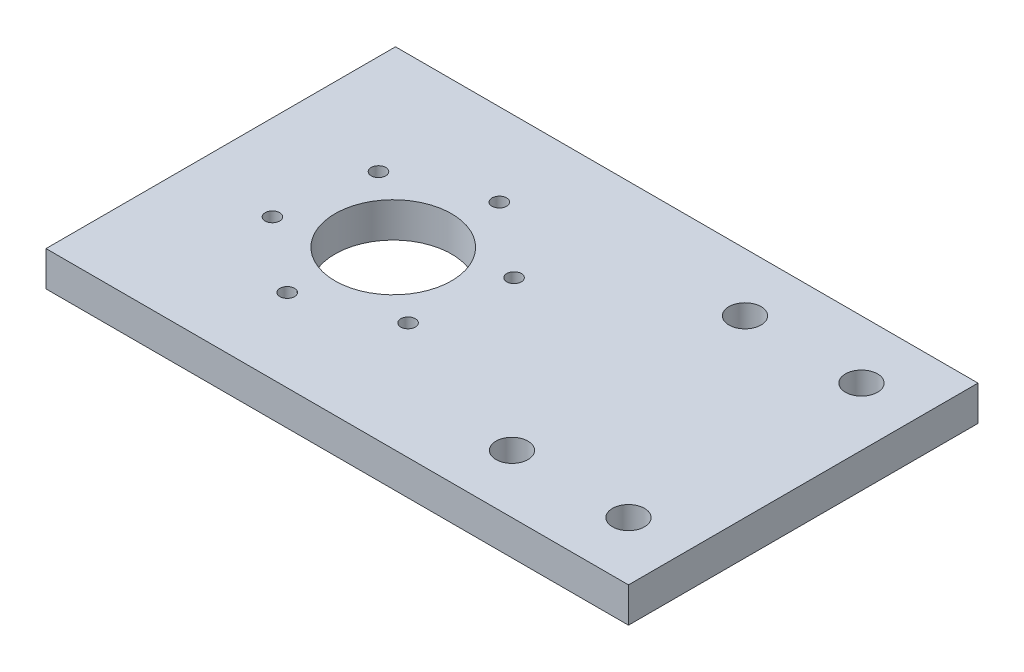
SolidWorks part; units mm, degrees
ref_plane "Front Plane" through (0, 0, 0) normal (0, 0, 1) x (1, 0, 0)
ref_plane "Top Plane" through (0, 0, 0) normal (0, 1, 0) x (1, 0, 0)
ref_plane "Right Plane" through (0, 0, 0) normal (1, 0, 0) x (0, 0, -1)
sketch "Sketch1" plane through (0, 0, 0) normal (0, 1, 0) x (1, 0, 0)
  line L1 (0, 0) -> (100, 0)
  line L2 (0, 0) -> (0, 60)
  line L3 (0, 60) -> (100, 60)
  line L4 (100, 0) -> (100, 60)
  dimension "D1" = 100
  dimension "D2" = 60
extrude "Boss-Extrude1" add sketch "Sketch1" along normal blind 6
sketch "Sketch2" plane through (0, 6, 0) normal (0, 1, 0) x (1, 0, 0)
  line L1 (100, 0) -> (100, 60) construction
  line L7 (100, 30) -> (0, 30) construction
  line L8 (0, 60) -> (0, 0) construction
  circle A0 centre (29.6153, 30) radius 10
  circle A5 centre (70, 50) radius 2.75
  circle A6 centre (90, 50) radius 2.75
  circle A7 centre (70, 10) radius 2.75
  circle A8 centre (90, 10) radius 2.75
  point P7 (100, 30)
  dimension "D1" = 20
extrude "Cut-Extrude1" cut sketch "Sketch2" against normal blind 6
sketch "Sketch3" plane through (0, 6, 0) normal (0, 1, 0) x (1, 0, 0)
  circle A0 centre (31.9984, 45.8215) radius 1.25 construction
  circle A1 centre (31.9984, 45.8215) radius 1.25
  circle A2 centre (17.105, 39.9745) radius 1.25 construction
  circle A3 centre (17.105, 39.9745) radius 1.25
  circle A4 centre (44.5087, 35.847) radius 1.25 construction
  circle A5 centre (14.722, 24.153) radius 1.25 construction
  circle A6 centre (27.2323, 14.1785) radius 1.25 construction
  circle A7 centre (42.1257, 20.0255) radius 1.25 construction
  circle A8 centre (31.9984, 45.8215) radius 1.25
  circle A9 centre (44.5087, 35.847) radius 1.25
  circle A10 centre (17.105, 39.9745) radius 1.25
  circle A11 centre (14.722, 24.153) radius 1.25
  circle A12 centre (27.2323, 14.1785) radius 1.25
  circle A13 centre (42.1257, 20.0255) radius 1.25
extrude "Cut-Extrude2" cut sketch "Sketch3" against normal through all contours A1 | A9 | A13 | A12 | A11 | A3
